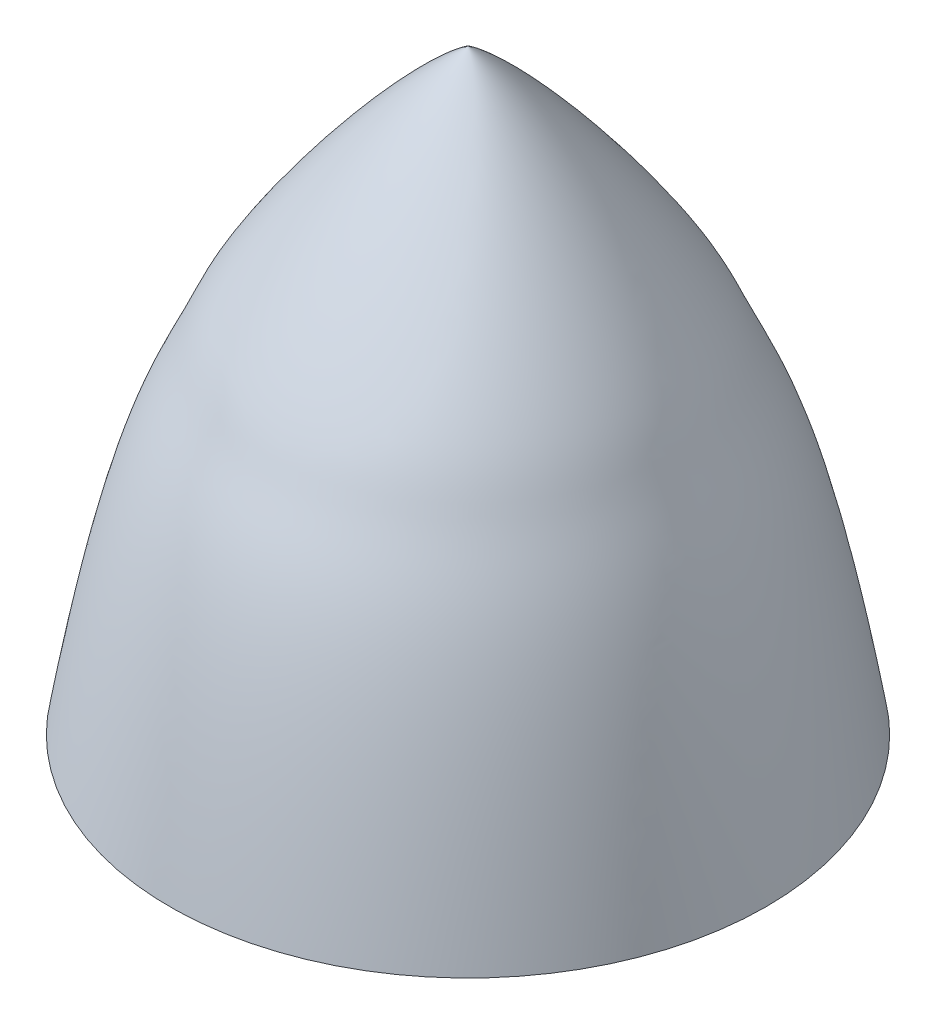
SolidWorks part; units mm, degrees
ref_plane "정면" through (0, 0, 0) normal (0, 0, 1) x (1, 0, 0)
ref_plane "윗면" through (0, 0, 0) normal (0, 1, 0) x (1, 0, 0)
ref_plane "우측면" through (0, 0, 0) normal (1, 0, 0) x (0, 0, -1)
sketch "스케치1" plane through (0, 0, 0) normal (0, 0, 1) x (1, 0, 0)
  line L0 (0, 0) -> (0, 19)
  line L1 (0, 0) -> (9.5, 0)
  line L2 (9.5, 0) -> (10.4549, -5.7065) construction
  line L3 (0, 19) -> (-1.6911, 20.1841) construction
  line L4 (0, 19) -> (0, 15.478) construction
  spline S0 degree 3 poles (0, 19) (1.8779, 17.6851) (5.5852, 12.9728) (7.2666, 8.9071) (8.2379, 7.5419) (9.5, 0) knots 0 0 0 0 0.402099 0.502099 1 1 1 1
  point P5 (0, 0)
  point P8 (6.0646, 10.6781)
  point P9 (12.3765, 10.0999)
  point P11 (6.6282, 11.7292)
  point P12 (6.8177, 10.4749)
  point P13 (6.202, 12.0303)
  point P14 (7.0121, 10.3453)
  point P15 (6.2992, 11.2202)
  dimension "D1" = 9.5
  dimension "D2" = 19
  dimension "D3" = 9.5
  dimension "D4" = 55
revolve "회전1" add sketch "스케치1" angle 360 about L0
